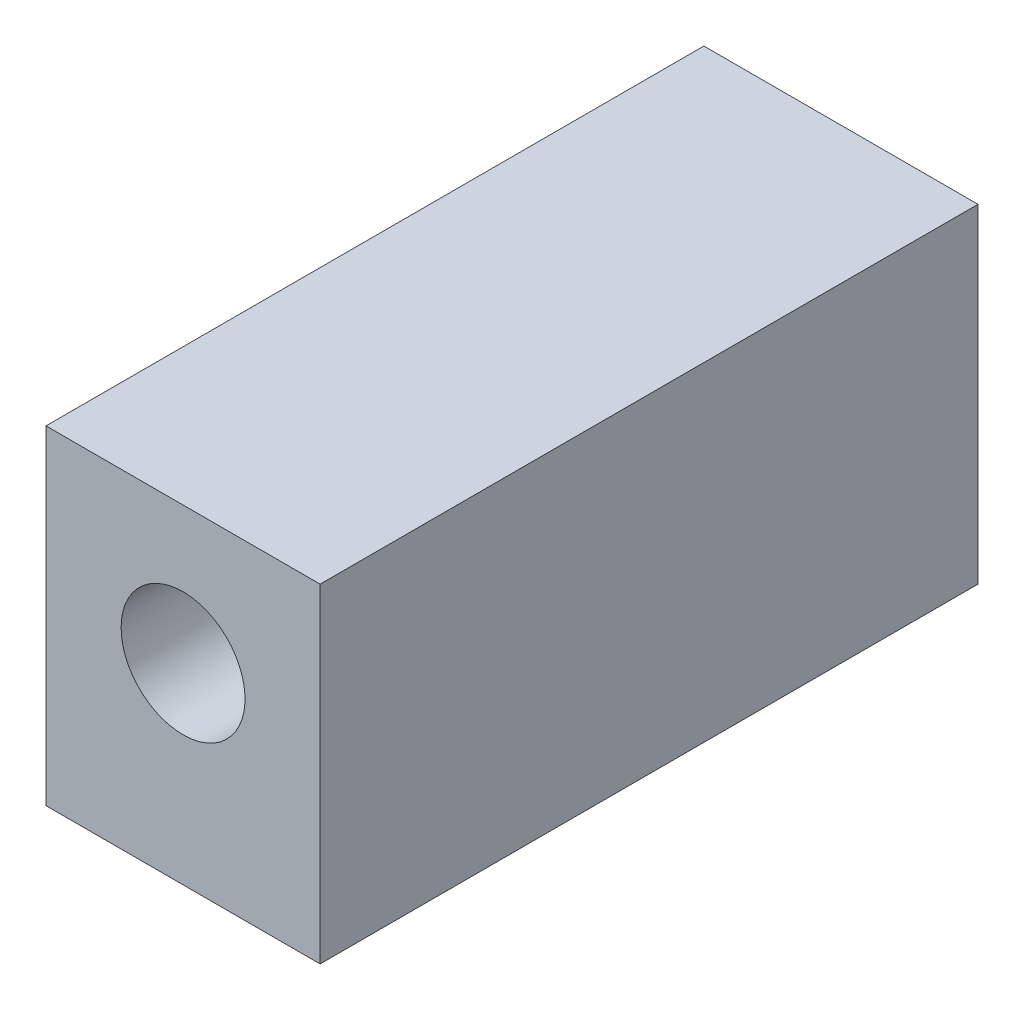
SolidWorks part; units mm, degrees
ref_plane "正面" through (0, 0, 0) normal (0, 0, 1) x (1, 0, 0)
ref_plane "平面" through (0, 0, 0) normal (0, 1, 0) x (1, 0, 0)
ref_plane "右側面" through (0, 0, 0) normal (1, 0, 0) x (0, 0, -1)
sketch "ｽｹｯﾁ1" plane through (0, 0, 0) normal (0, 0, 1) x (1, 0, 0)
  line L1 (-10.5821, 11.8684) -> (14.4179, 11.8684)
  line L2 (-10.5821, 11.8684) -> (-10.5821, -18.1316)
  line L3 (-10.5821, -18.1316) -> (14.4179, -18.1316)
  line L4 (14.4179, 11.8684) -> (14.4179, -18.1316)
  dimension "D1" = 25
  dimension "D2" = 30
extrude "ﾎﾞｽ - 押し出し1" add sketch "ｽｹｯﾁ1" along normal blind 60
sketch "ｽｹｯﾁ2" plane through (0, 0, 0) normal (0, 0, -1) x (-1, 0, 0)
  line L0 (10.5821, 11.8684) -> (10.5821, -18.1316) construction
  line L1 (-14.4179, 11.8684) -> (10.5821, 11.8684) construction
  circle A0 centre (-1.9179, -0.6316) radius 9.6
  dimension "D3" = 19.2
  dimension "D1" = 12.5
  dimension "D2" = 12.5
extrude "ｶｯﾄ - 押し出し1" cut sketch "ｽｹｯﾁ2" against normal blind 47.5
sketch "ｽｹｯﾁ3" plane through (0, 0, 47.5) normal (0, 0, -1) x (-1, 0, 0)
  line L0 (10.5821, 11.8684) -> (10.5821, -18.1316) construction
  line L1 (-14.4179, 11.8684) -> (10.5821, 11.8684) construction
  circle A0 centre (-1.9179, -0.6316) radius 5.65
  dimension "D1" = 11.3
  dimension "D2" = 12.5
  dimension "D3" = 12.5
extrude "ｶｯﾄ - 押し出し2" cut sketch "ｽｹｯﾁ3" against normal through all
